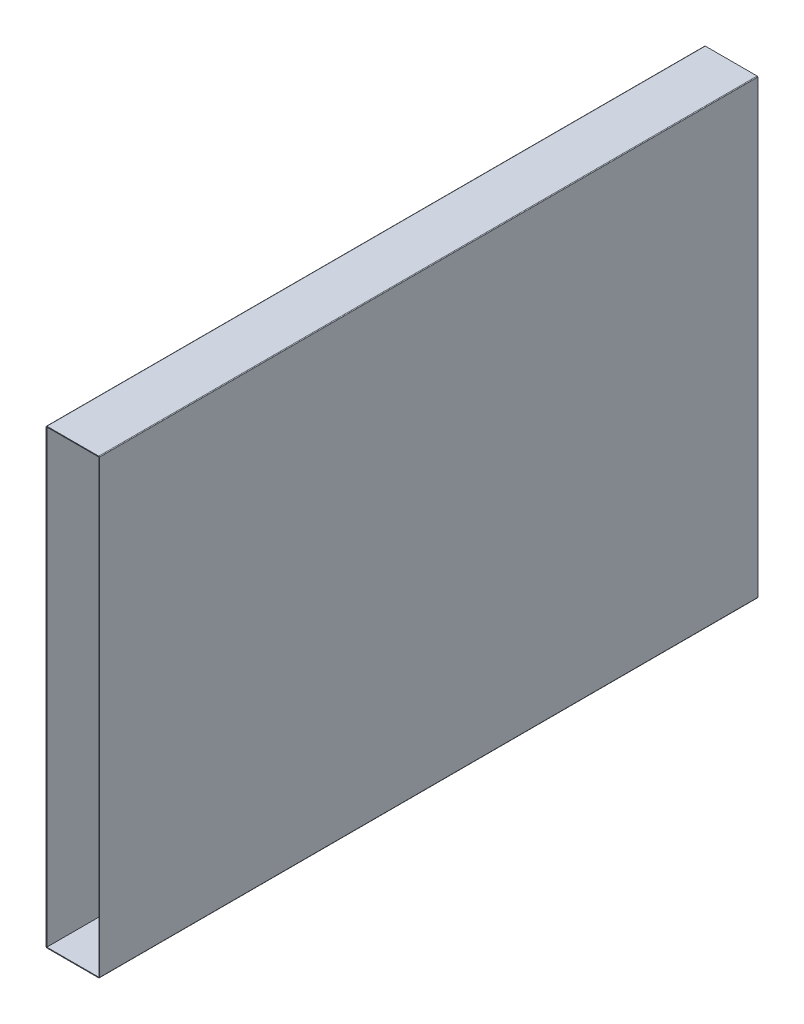
SolidWorks part; units mm, degrees
material "Plastique personnalisé"
ref_plane "Plan de face" through (0, 0, 0) normal (0, 0, 1) x (1, 0, 0)
ref_plane "Plan de dessus" through (0, 0, 0) normal (0, 1, 0) x (1, 0, 0)
ref_plane "Plan de droite" through (0, 0, 0) normal (1, 0, 0) x (0, 0, -1)
sketch "Esquisse1" plane through (0, 0, 0) normal (0, 0, 1) x (1, 0, 0)
  line L0 (182.5, 60.6447) -> (197.5, -69.3553) construction
  line L1 (182.5, 60.6447) -> (197.5, 60.6447)
  line L2 (182.5, 60.6447) -> (182.5, -69.3553)
  line L3 (182.5, -69.3553) -> (197.5, -69.3553)
  line L4 (197.5, 60.6447) -> (197.5, -69.3553)
  line L6 (182.5365, -69.5567) -> (197.4635, -69.5567)
  line L7 (182.3365, -69.3567) -> (182.3365, 60.6461)
  line L8 (182.5365, 60.8461) -> (197.4635, 60.8461)
  line L9 (197.6635, -69.3567) -> (197.6635, 60.6461)
  line L10 (182.3365, -69.5567) -> (197.6635, 60.8461) construction
  line L11 (182.3365, 60.8461) -> (197.6635, -69.5567) construction
  arc A0 (197.4635, -69.5567) -> (197.6635, -69.3567) centre (197.4635, -69.3567) ccw
  arc A1 (182.5365, -69.5567) -> (182.3365, -69.3567) centre (182.5365, -69.3567) cw
  arc A2 (182.3365, 60.6461) -> (182.5365, 60.8461) centre (182.5365, 60.6461) cw
  arc A3 (197.4635, 60.8461) -> (197.6635, 60.6461) centre (197.4635, 60.6461) cw
  point P6 (190, -4.3553)
  dimension "D1" = 0.2
extrude "Boss.-Extru.1" add sketch "Esquisse1" along normal blind 190
